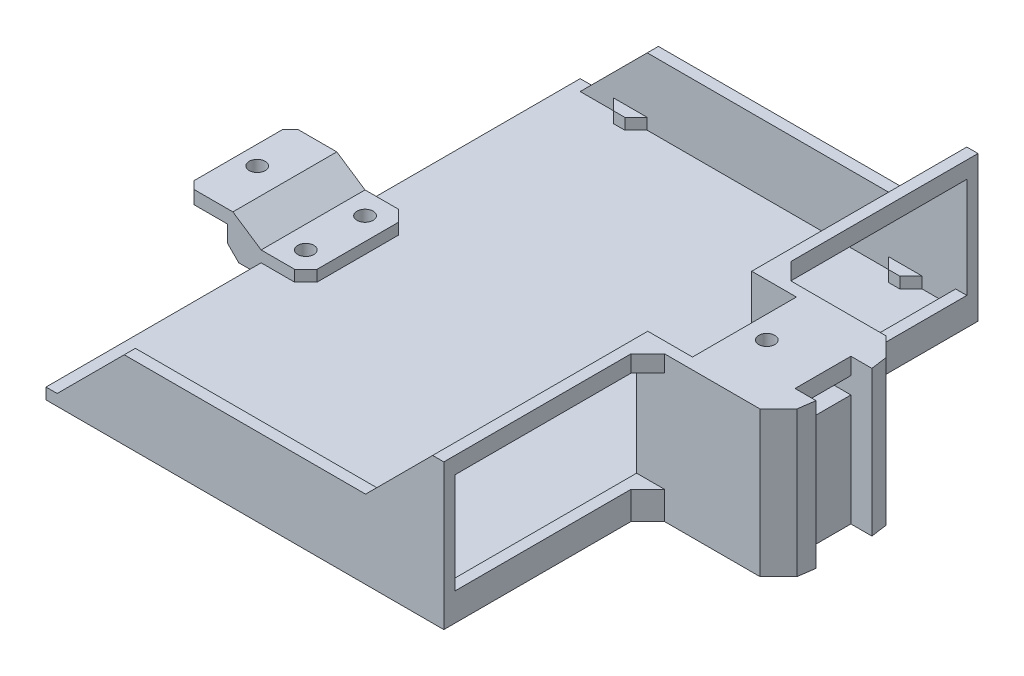
SolidWorks part; units mm, degrees
ref_plane "Front Plane" through (0, 0, 0) normal (0, 0, 1) x (1, 0, 0)
ref_plane "Top Plane" through (0, 0, 0) normal (0, 1, 0) x (1, 0, 0)
ref_plane "Right Plane" through (0, 0, 0) normal (1, 0, 0) x (0, 0, -1)
sketch "Sketch1" plane through (0, 0, 0) normal (0, 1, 0) x (1, 0, 0)
  line L0 (-1000, 0) -> (49000, 0) construction
  line L1 (6.35, -70.6772) -> (-6.35, -70.6772)
  line L2 (70.231, 6.35) -> (75.935, 6.35) construction
  line L3 (70.231, 6.35) -> (70.231, -6.35) construction
  line L4 (70.231, -6.35) -> (75.935, -6.35) construction
  line L5 (75.935, 6.35) -> (75.935, -6.35) construction
  line L6 (70.6772, 6.35) -> (75.4524, 6.35)
  line L7 (70.6772, 6.35) -> (70.6772, -6.35)
  line L8 (70.6772, -6.35) -> (75.4524, -6.35)
  line L9 (75.4524, 6.35) -> (75.4524, -6.35)
  line L10 (6.35, -70.6772) -> (6.35, -75.4524)
  line L11 (6.35, -75.4524) -> (-6.35, -75.4524)
  line L12 (-6.35, -70.6772) -> (-6.35, -75.4524)
  line L13 (-70.6772, -6.35) -> (-70.6772, 6.35)
  line L14 (-70.6772, -6.35) -> (-75.4524, -6.35)
  line L15 (-75.4524, -6.35) -> (-75.4524, 6.35)
  line L16 (-70.6772, 6.35) -> (-75.4524, 6.35)
  line L17 (-6.35, 70.6772) -> (6.35, 70.6772)
  line L18 (-6.35, 70.6772) -> (-6.35, 75.4524)
  line L19 (-6.35, 75.4524) -> (6.35, 75.4524)
  line L20 (6.35, 70.6772) -> (6.35, 75.4524)
  circle A0 centre (0, 0) radius 75.692 construction
  circle A1 centre (0, 0) radius 76.2 construction
  circle A2 centre (0, 0) radius 70.231 construction
  point P10 (75.935, 0)
  point P31 (0, 0)
  dimension "D1" = 151.384
  dimension "D2" = 152.4
  dimension "D5" = 140.462
  dimension "D3" = 12.7
  dimension "D4" = 0.4826
  dimension "D6" = 4.7752
  dimension "D7" = 4
sketch "Sketch3" plane through (0, 0, 0) normal (0, 1, 0) x (1, 0, 0)
  line L1 (-45.2113, -60.706) -> (45.2113, -60.706)
  line L2 (-45.2113, -60.706) -> (-45.2113, 60.706)
  line L3 (-45.2113, 60.706) -> (45.2113, 60.706)
  line L4 (45.2113, -60.706) -> (45.2113, 60.706)
  line L5 (-45.2113, -60.706) -> (45.2113, 60.706) construction
  line L6 (-45.2113, 60.706) -> (45.2113, -60.706) construction
  circle A0 centre (0, 0) radius 75.692 construction
  point P0 (0, 0)
  dimension "D1" = 121.412
extrude "Boss-Extrude4" add sketch "Sketch3" along normal blind 2.54
sketch "Sketch6" plane through (0, 2.54, 0) normal (0, 1, 0) x (1, 0, 0)
  line L0 (-1000, 0) -> (49000, 0) construction
  line L1 (45.2113, -60.706) -> (45.2113, 60.706) construction
  line L2 (45.2113, 60.706) -> (-45.2113, 60.706) construction
  line L3 (45.2113, -60.706) -> (45.2113, 60.706)
  line L4 (45.2113, 60.706) -> (-45.2113, 60.706)
  line L5 (-45.2113, 60.706) -> (-45.2113, 58.166)
  line L6 (-45.2113, 60.706) -> (-45.2113, -60.706) construction
  line L7 (-45.2113, 58.166) -> (42.6713, 58.166)
  line L8 (42.6713, 58.166) -> (42.6713, -58.166)
  line L10 (-45.2113, -58.166) -> (42.6713, -58.166)
  line L11 (-45.2113, -60.706) -> (-45.2113, -58.166)
  line L12 (45.2113, -60.706) -> (-45.2113, -60.706)
  dimension "D1" = 2.54
  dimension "D2" = 2.54
extrude "Boss-Extrude5" add sketch "Sketch6" along normal blind 30.48
sketch "Sketch7" plane through (0, 0, 60.706) normal (0, 0, 1) x (1, 0, 0)
  line L0 (42.6713, 2.54) -> (-45.2113, 2.54) construction
  line L1 (42.6713, 33.02) -> (42.6713, 2.54) construction
  line L2 (42.6713, 2.54) -> (-45.2113, 2.54) construction
  line L3 (42.6713, 33.02) -> (42.6713, 2.54) construction
  line L4 (0, -1000) -> (0, 49000) construction
  line L5 (-957.3287, 17.78) -> (49042.6713, 17.78) construction
  line L6 (-42.6713, 33.02) -> (-42.6713, 2.54) construction
  line L7 (-42.6713, 2.54) -> (-27.4313, 17.78)
  line L8 (-27.4313, 17.78) -> (27.4313, 17.78)
  line L9 (27.4313, 17.78) -> (42.6713, 33.02)
  line L10 (42.6713, 33.02) -> (-45.2113, 33.02)
  line L11 (-45.2113, 33.02) -> (-45.2113, 2.54)
  line L12 (-45.2113, 2.54) -> (-42.6713, 2.54)
  point P9 (42.6713, 17.78)
  dimension "D1" = 45
  dimension "D2" = 45
extrude "Cut-Extrude2" cut sketch "Sketch7" against normal through all
sketch "Sketch8" plane through (0, 0, 0) normal (0, 1, 0) x (1, 0, 0)
  line L0 (-1000, 0) -> (49000, 0) construction
  line L1 (45.2113, 14.351) -> (70.694, 14.351)
  line L2 (45.2113, -60.706) -> (45.2113, 60.706) construction
  line L3 (70.694, 14.351) -> (74.9221, 10.1229)
  line L4 (74.9221, 10.1229) -> (75.4524, 6.35)
  line L5 (75.4524, 6.35) -> (70.6772, 6.35)
  line L6 (70.6772, 6.35) -> (70.6772, -6.35)
  line L7 (45.2113, 14.351) -> (45.2113, -14.351)
  line L8 (45.2113, -14.351) -> (70.694, -14.351)
  line L9 (70.694, -14.351) -> (74.9221, -10.1229)
  line L10 (74.9221, -10.1229) -> (75.4524, -6.35)
  line L11 (75.4524, -6.35) -> (70.6772, -6.35)
  line L13 (70.6772, 6.35) -> (70.6772, -6.35) construction
  line L14 (70.6772, 6.35) -> (75.4524, 6.35) construction
  point P13 (45.2113, 0)
  point P17 (70.6772, 0)
  dimension "D1" = 82
  dimension "D2" = 135
  dimension "D3" = 28.702
  dimension "D4" = 3.81
extrude "Boss-Extrude6" add sketch "Sketch8" along normal up to surface (33.02 mm away) up to face at (43.518, 33.02, 0)
sketch "Sketch9" plane through (0, 33.02, 0) normal (0, 1, 0) x (1, 0, 0)
  line L0 (-1000, 0) -> (49000, 0) construction
  line L1 (52.8313, -11.811) -> (52.8313, 11.811)
  line L2 (52.8313, 11.811) -> (42.6713, 11.811)
  line L3 (42.6713, 58.166) -> (42.6713, -58.166) construction
  line L4 (42.6713, 11.811) -> (42.6713, -11.811)
  line L5 (52.8313, -11.811) -> (42.6713, -11.811)
  line L6 (70.694, 14.351) -> (45.2113, 14.351) construction
  point P10 (42.6713, 0)
  point P11 (52.8313, 0)
  dimension "D1" = 10.16
  dimension "D2" = 2.54
extrude "Cut-Extrude3" cut sketch "Sketch9" against normal offset from surface (27.94 mm away) 2.54 up to face at (-21.9706, 2.54, 0)
sketch "Sketch11" plane through (0, 2.54, 0) normal (0, 1, 0) x (1, 0, 0)
  line L5 (35.0513, 58.166) -> (27.4313, 58.166)
  line L6 (-42.6713, 58.166) -> (42.6713, 58.166) construction
  line L7 (27.4313, 58.166) -> (29.9713, 55.626)
  line L8 (29.9713, 55.626) -> (32.5113, 55.626)
  line L9 (32.5113, 55.626) -> (35.0513, 58.166)
  line L10 (42.6713, 58.166) -> (42.6713, -58.166) construction
  line L11 (-1000, 0) -> (49000, 0) construction
  line L12 (0, -1000) -> (0, 49000) construction
  line L13 (-29.9713, 55.626) -> (-32.5113, 55.626)
  line L14 (-27.4313, 58.166) -> (-29.9713, 55.626)
  line L15 (-35.0513, 58.166) -> (-27.4313, 58.166)
  line L16 (-32.5113, 55.626) -> (-35.0513, 58.166)
  line L17 (29.9713, -55.626) -> (32.5113, -55.626)
  line L18 (27.4313, -58.166) -> (29.9713, -55.626)
  line L19 (35.0513, -58.166) -> (27.4313, -58.166)
  line L20 (32.5113, -55.626) -> (35.0513, -58.166)
  line L21 (-27.4313, -58.166) -> (-29.9713, -55.626)
  line L22 (-35.0513, -58.166) -> (-27.4313, -58.166)
  line L23 (-32.5113, -55.626) -> (-35.0513, -58.166)
  line L24 (-29.9713, -55.626) -> (-32.5113, -55.626)
  dimension "D1" = 45
  dimension "D2" = 45
  dimension "D3" = 2.54
  dimension "D4" = 2.54
  dimension "D5" = 7.62
extrude "Boss-Extrude7" add sketch "Sketch11" along normal up to surface (2.54 mm away) up to face at (47.7513, 5.08, 0)
sketch "Sketch12" plane through (52.8313, 0, 0) normal (-1, 0, 0) x (0, 0, 1)
  line L0 (11.811, 5.08) -> (11.811, 33.02) construction
  line L1 (11.811, 29.21) -> (-11.811, 29.21)
  line L2 (11.811, 29.21) -> (11.811, 25.4)
  line L3 (11.811, 25.4) -> (-11.811, 25.4)
  line L4 (-11.811, 29.21) -> (-11.811, 25.4)
  line L5 (-11.811, 5.08) -> (-11.811, 33.02) construction
  line L6 (11.811, 33.02) -> (-11.811, 33.02) construction
  dimension "D1" = 3.81
  dimension "D2" = 3.81
extrude "Cut-Extrude4" cut sketch "Sketch12" against normal blind 10.16
sketch "Sketch13" plane through (62.9913, 0, 0) normal (-1, 0, 0) x (0, 0, 1)
  line L0 (11.811, 29.21) -> (-11.811, 29.21) construction
  line L1 (-6.35, 29.21) -> (6.35, 29.21)
  line L2 (-6.35, 29.21) -> (-6.35, 25.4)
  line L3 (-6.35, 25.4) -> (6.35, 25.4)
  line L4 (6.35, 29.21) -> (6.35, 25.4)
  line L5 (-6.35, 33.02) -> (-6.35, 0) construction
  line L6 (-11.811, 25.4) -> (11.811, 25.4) construction
  line L7 (6.35, 33.02) -> (6.35, 0) construction
extrude "Cut-Extrude5" cut sketch "Sketch13" against normal through all
sketch "Sketch15" plane through (0, 0, 0) normal (0, 0, 1) x (1, 0, 0)
  line L0 (0, -1000) -> (0, 49000) construction
  line L2 (62.9913, 29.21) -> (62.9913, 25.4) construction
  line L3 (62.9913, 25.4) -> (52.8313, 25.4) construction
  line L4 (62.9913, 29.21) -> (52.8313, 29.21) construction
  line L5 (62.9913, 25.4) -> (52.8313, 25.4) construction
  line L6 (62.9913, 29.21) -> (62.9913, 25.4) construction
  line L7 (62.9913, 29.21) -> (52.8313, 29.21) construction
  line L8 (-62.9913, 29.21) -> (-52.8313, 29.21) construction
  line L9 (-62.9913, 29.21) -> (-62.9913, 25.4) construction
  line L10 (-62.9913, 25.4) -> (-52.8313, 25.4) construction
  line L11 (-998.1426, 17.78) -> (49001.8574, 17.78) construction
  line L13 (-62.9913, 10.16) -> (-52.8313, 10.16)
  line L14 (-62.9913, 6.35) -> (-62.9913, 10.16)
  line L15 (-62.9913, 6.35) -> (-52.8313, 6.35)
  line L16 (-27.4313, 17.78) -> (27.4313, 17.78) construction
  line L17 (-52.8313, 6.35) -> (-52.8313, 0)
  line L18 (-52.8313, 0) -> (-45.2113, 0)
  line L19 (-45.2113, 0) -> (-45.2113, 2.54)
  line L20 (-45.2113, 2.54) -> (-35.0513, 2.54)
  line L21 (-35.0513, 2.54) -> (-42.6713, 2.54) construction
  line L23 (-35.0513, 2.54) -> (-35.0513, 5.08)
  line L24 (-35.0513, 5.08) -> (-45.2113, 5.08)
  line L25 (-45.2113, 5.08) -> (-52.8313, 10.16)
  line L26 (-27.4313, 5.08) -> (-35.0513, 5.08) construction
  line L27 (52.8313, 5.08) -> (42.6713, 5.08) construction
  line L28 (52.8313, 5.08) -> (42.6713, 5.08) construction
extrude "Boss-Extrude9" add sketch "Sketch15" against normal up to surface and the other way up to surface up to face at (52.8313, 23.1775, -11.811) other way up to face at (52.8313, 23.1775, 11.811)
hole_wizard "CBORE for #6 Pan Head Machine Screw1" positions "Sketch16" profile "Sketch17" counterbore size "#6" standard "ANSI Inch" end condition through all
sketch "Sketch16" plane through (0, 0, 0) normal (0, -1, 0) x (-1, 0, 0)
  line L0 (-47.7513, -988.189) -> (-47.7513, 49011.811) construction
  line L1 (-52.8313, 11.811) -> (-42.6713, 11.811) construction
  line L2 (-1000, 0) -> (49000, 0) construction
  line L3 (40.1313, -988.189) -> (40.1313, 49011.811) construction
  line L4 (45.2113, 11.811) -> (35.0513, 11.811) construction
  line L5 (-1047.7513, 6.731) -> (48952.2487, 6.731) construction
  line L6 (-1047.7513, -6.731) -> (48952.2487, -6.731) construction
  line L7 (-52.8313, 11.811) -> (-42.6713, 1.651) construction
  line L8 (-42.6713, 11.811) -> (-42.6713, -11.811) construction
  point P0 (-47.7513, 6.731)
  point P7 (-47.7513, 11.811)
  point P18 (-47.7513, -6.731)
  point P24 (40.1313, 11.811)
  point P34 (40.1313, 6.731)
  point P36 (40.1313, -6.731)
  dimension "D1" = 45
sketch "Sketch17" plane through (47.7513, 0, -6.731) normal (1, 0, 0) x (0, 0, -1)
  line L0 (0, 0) -> (0, 33.02)
  line L1 (0, 33.02) -> (1.8288, 33.02)
  line L3 (1.8288, 33.02) -> (1.8288, 2.4638)
  line L4 (1.8288, 2.4638) -> (3.7706, 2.4638)
  line L5 (3.7706, 2.4638) -> (3.7706, 0)
  line L7 (3.7706, 0) -> (0, 0)
  line L11 (0, -6.35) -> (0, 107.95) construction
  dimension "Thru Hole Dia." = 3.6576
  dimension "Thru Hole Depth" = 33.02
  dimension "C'Bore Dia." = 7.5413
  dimension "C'Bore Depth" = 2.4638
hole_wizard "#6 Clearance Hole1" positions "Sketch19" profile "Sketch20" hole size "#6" standard "ANSI Inch" end condition through all
sketch "Sketch19" plane through (0, 33.02, 0) normal (0, 1, 0) x (1, 0, 0)
  line L0 (-1000, 0) -> (49000, 0) construction
  line L1 (0, -1000) -> (0, 49000) construction
  line L2 (57.9113, -988.189) -> (57.9113, 49011.811) construction
  line L3 (62.9913, 11.811) -> (52.8313, 11.811) construction
  point P6 (57.9113, 0)
  point P13 (-57.9113, 0)
  point P20 (57.9113, 11.811)
sketch "Sketch20" plane through (-57.9113, 33.02, 0) normal (1, 0, 0) x (0, 0, 1)
  line L0 (0, 0) -> (0, 33.02)
  line L1 (0, 33.02) -> (1.8288, 33.02)
  line L2 (1.8288, 33.02) -> (1.8288, 0)
  line L5 (1.8288, 0) -> (0, 0)
  line L11 (0, -6.35) -> (0, 107.95) construction
  dimension "Thru Hole Dia." = 3.6576
  dimension "Thru Hole Depth" = 33.02
sketch "Sketch21" plane through (42.6713, 0, 0) normal (-1, 0, 0) x (0, 0, 1)
  line L0 (-1058.166, 17.78) -> (48941.834, 17.78) construction
  line L1 (-58.166, 33.02) -> (-58.166, 2.54) construction
  line L2 (0, -1000) -> (0, 49000) construction
  line L3 (-11.811, 0) -> (11.811, 0) construction
  line L9 (-1008.4655, 5.08) -> (48991.5345, 5.08) construction
  line L10 (-58.166, 6.35) -> (-58.166, 29.21)
  line L11 (-11.811, 5.08) -> (11.811, 5.08) construction
  line L14 (-58.166, 29.21) -> (-14.351, 29.21)
  line L15 (-14.351, 29.21) -> (-14.351, 6.35)
  line L18 (-58.166, 6.35) -> (-14.351, 6.35)
  line L20 (58.166, 29.21) -> (14.351, 29.21)
  line L21 (58.166, 6.35) -> (58.166, 29.21)
  line L22 (58.166, 6.35) -> (14.351, 6.35)
  line L23 (14.351, 29.21) -> (14.351, 6.35)
  line L24 (-58.166, 33.02) -> (-58.166, 17.78) construction
  line L25 (-14.351, 33.02) -> (-14.351, 0) construction
  point P5 (-58.166, 17.78)
  point P10 (0, 0)
  point P19 (-14.351, 17.78)
  point P20 (-58.166, 17.78)
  dimension "D1" = 1.27
extrude "Cut-Extrude6" cut sketch "Sketch21" against normal through all
chamfer "Chamfer1" distance 2.54 angle 45 5 edges at (-62.9913, 8.255, -11.811) (-62.9913, 8.255, 11.811) (-35.0513, 3.81, 11.811) (-35.0513, 3.81, -11.811) (-52.8313, 0, 0)
chamfer "Chamfer2" distance 3.81 angle 45 4 edges at (45.2113, 3.175, -14.351) (45.2113, 3.175, 14.351) (45.2113, 31.115, -14.351) (45.2113, 31.115, 14.351)
sketch "Sketch22" plane through (0, 10.16, 0) normal (0, 1, 0) x (1, 0, 0)
  line L0 (-62.9913, 9.271) -> (-62.9913, -9.271) construction
  line L1 (-45.2113, 11.811) -> (-62.9913, 11.811)
  line L2 (-45.2113, 11.811) -> (-45.2113, -11.811)
  line L3 (-45.2113, -11.811) -> (-62.9913, -11.811)
  line L4 (-62.9913, 11.811) -> (-62.9913, -11.811)
  point P5 (-45.2113, -11.811)
extrude "Cut-Extrude7" cut sketch "Sketch22" against normal blind 0.8
chamfer "Chamfer3" distance 0.8 angle 45 1 edges at (-62.9913, 9.36, 0)
